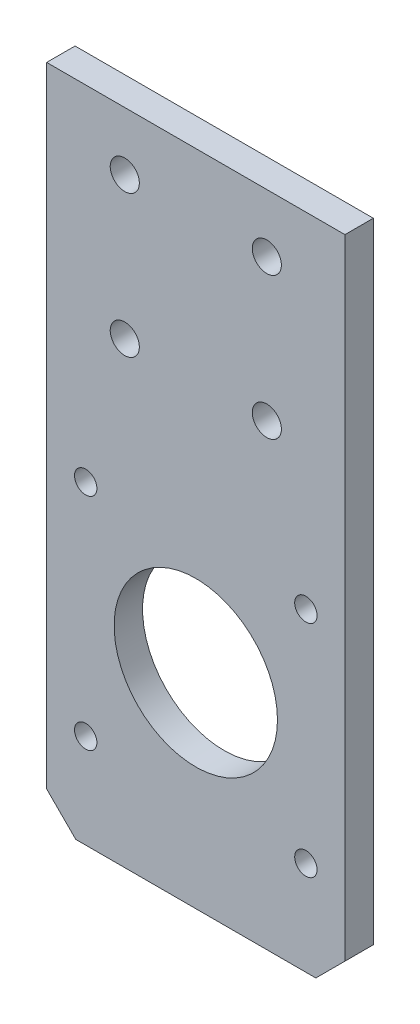
SolidWorks part; units mm, degrees
ref_plane "Alzado" through (0, 0, 0) normal (0, 0, 1) x (1, 0, 0)
ref_plane "Planta" through (0, 0, 0) normal (0, 1, 0) x (1, 0, 0)
ref_plane "Vista lateral" through (0, 0, 0) normal (1, 0, 0) x (0, 0, -1)
sketch "Croquis1" plane through (0, 0, 0) normal (0, 0, 1) x (1, 0, 0)
  line L0 (11, 56.8) -> (31, 76.8) construction
  line L1 (0, 85) -> (42, 85)
  line L2 (0, 85) -> (0, 0)
  line L3 (0, 0) -> (42, 0)
  line L4 (42, 85) -> (42, 0)
  line L5 (21, 66.8) -> (21, 85) construction
  circle A0 centre (11, 76.8) radius 2.05
  circle A1 centre (31, 76.8) radius 2.05
  circle A4 centre (31, 56.8) radius 2.05
  circle A5 centre (11, 56.8) radius 2.05
  circle A6 centre (21, 21.08) radius 2.55
  dimension "D3" = 4.1
  dimension "D11" = 5.1
  dimension "D1" = 42
  dimension "D2" = 85
  dimension "D4" = 20
  dimension "D5" = 63.92
  dimension "D6" = 8.2
  dimension "D7" = 20
extrude "Saliente-Extruir1" add sketch "Croquis1" along normal blind 4
sketch "Croquis5" plane through (0, 0, 4) normal (0, 0, 1) x (1, 0, 0)
  line L0 (5.5, 36.58) -> (36.5, 5.58) construction
  line L2 (36.5, 36.58) -> (5.5, 5.58) construction
  circle A0 centre (21, 21.08) radius 11.5
  circle A1 centre (5.5, 36.58) radius 1.575
  circle A2 centre (36.5, 36.58) radius 1.575
  circle A3 centre (36.5, 5.58) radius 1.575
  circle A4 centre (5.5, 5.58) radius 1.575
  dimension "D1" = 23
  dimension "D4" = 3.15
  dimension "D2" = 31
  dimension "D3" = 31
extrude "Cortar-Extruir2" cut sketch "Croquis5" against normal through all
sketch "Croquis7" plane through (0, 0, 4) normal (0, 0, 1) x (1, 0, 0)
  line L1 (0, 0) -> (42, 0)
  line L2 (0, 0) -> (0, -7.7)
  line L3 (0, -7.7) -> (42, -7.7)
  line L4 (42, 0) -> (42, -7.7)
  dimension "D1" = 7.7
extrude "Saliente-Extruir2" add sketch "Croquis7" against normal through all
chamfer "Chaflán1" distance 4.1 angle 45 2 edges at (42, -7.7, 2) (0, -7.7, 2)
